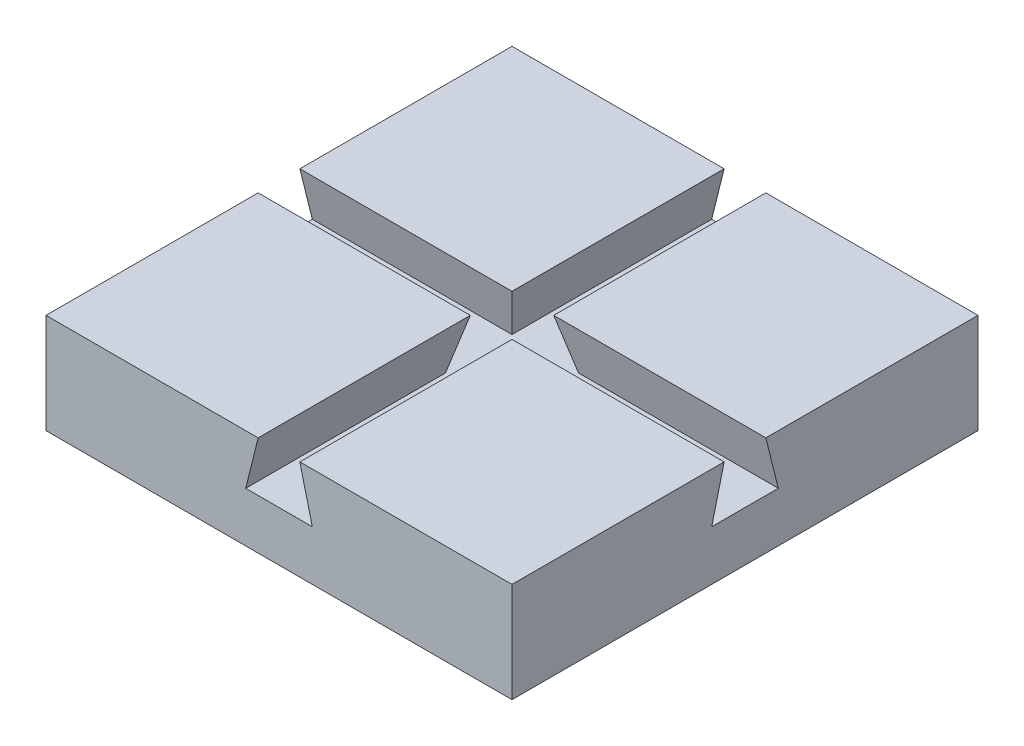
SolidWorks part; units mm, degrees
material "PW40:11:Ar:0:-1:Re:14:Ts:15:16:17:18:19:20:"
ref_plane "Front" through (0, 0, 0) normal (0, 0, 1) x (1, 0, 0)
ref_plane "Top" through (0, 0, 0) normal (0, 1, 0) x (1, 0, 0)
ref_plane "Right" through (0, 0, 0) normal (1, 0, 0) x (0, 0, -1)
sketch "Sketch1" plane through (0, 0, 0) normal (0, 1, 0) x (1, 0, 0)
  line L0 (-44.45, -44.45) -> (44.45, -44.45)
  line L1 (-44.45, -44.45) -> (-44.45, 44.45)
  line L2 (44.45, 44.45) -> (-44.45, 44.45)
  line L3 (44.45, 44.45) -> (44.45, -44.45)
  line L4 (-44.45, -44.45) -> (44.45, 44.45) construction
  dimension "D1" = 88.9
extrude "Base-Extrude" add sketch "Sketch1" along normal blind 19.05
sketch "Sketch2" plane through (0, 0, 44.45) normal (0, 0, 1) x (1, 0, 0)
  line L0 (0, -6.2714) -> (0, 26.7115) construction
  line L1 (6.35, 9.525) -> (-6.35, 9.525)
  line L2 (-6.35, 9.525) -> (-3.9752, 19.05)
  line L3 (-44.45, 19.05) -> (44.45, 19.05) construction
  line L4 (6.35, 9.525) -> (3.9752, 19.05)
  line L5 (-3.9752, 19.05) -> (3.9752, 19.05)
  point P6 (0, 9.525)
  point P11 (0, 19.05)
  dimension "D1" = 28
  dimension "D2" = 9.525
  dimension "D3" = 12.7
extrude "Cut-Extrude1" cut sketch "Sketch2" against normal through all
sketch "Sketch3" plane through (44.45, -3.5382, -0.6646) normal (1, 0, 0) x (0, 0, -1)
  line L0 (-0.6646, -6.2714) -> (-0.6646, 26.7115) construction
  line L1 (5.6854, 13.0632) -> (-7.0146, 13.0632)
  line L2 (-7.0146, 13.0632) -> (-4.6397, 22.5882)
  line L3 (43.7854, 22.5882) -> (-45.1146, 22.5882) construction
  line L4 (5.6854, 13.0632) -> (3.3106, 22.5882)
  line L5 (-4.6397, 22.5882) -> (3.3106, 22.5882)
  point P6 (-0.6646, 13.0632)
  point P11 (-0.6646, 22.5882)
  dimension "D1" = 28
  dimension "D2" = 9.525
  dimension "D3" = 12.7
extrude "Cut-Extrude2" cut sketch "Sketch3" against normal through all
